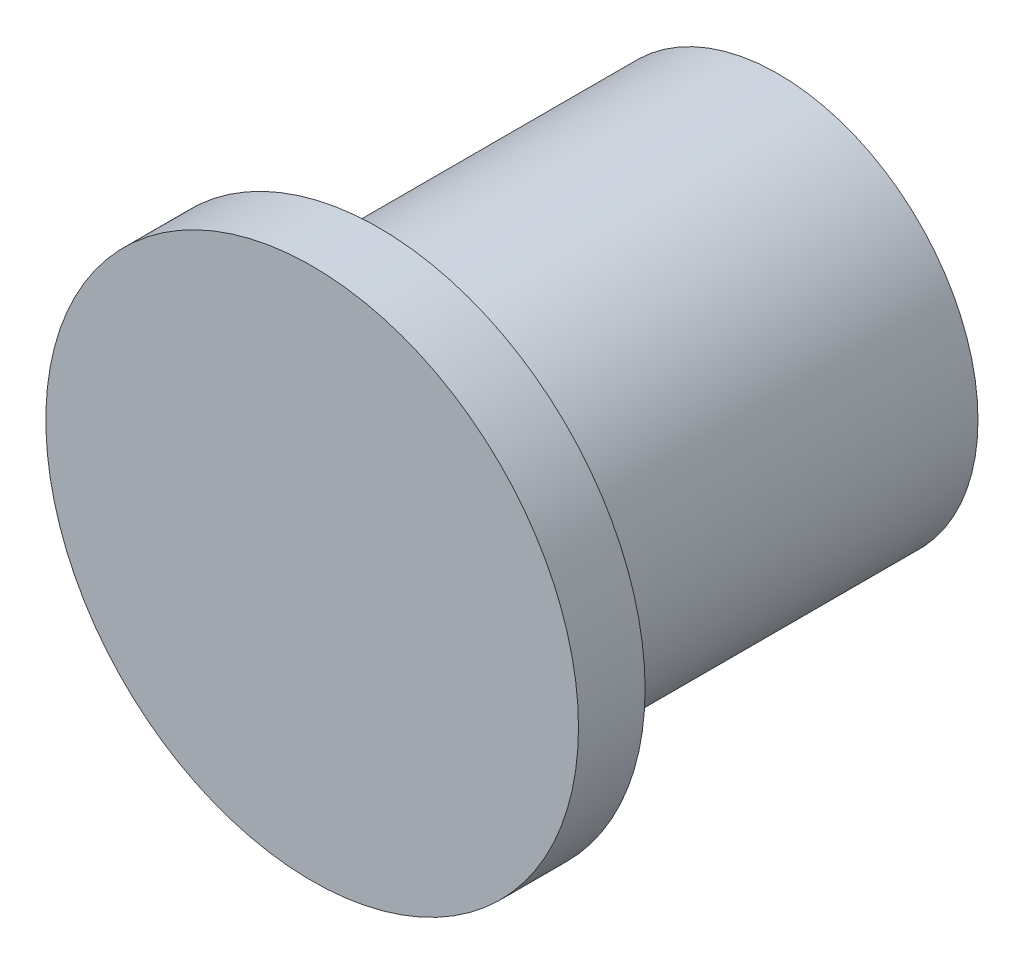
SolidWorks part; units mm, degrees
ref_plane "Front Plane" through (0, 0, 0) normal (0, 0, 1) x (1, 0, 0)
ref_plane "Top Plane" through (0, 0, 0) normal (0, 1, 0) x (1, 0, 0)
ref_plane "Right Plane" through (0, 0, 0) normal (1, 0, 0) x (0, 0, -1)
sketch "Sketch1" plane through (0, 0, 0) normal (0, 0, 1) x (1, 0, 0)
  circle A0 centre (0, 0) radius 76.2
  dimension "D1" = 152.4
extrude "Boss-Extrude1" add sketch "Sketch1" along normal blind 152.4
sketch "Sketch2" plane through (0, 0, 152.4) normal (0, 0, 1) x (1, 0, 0)
  circle A0 centre (0, 0) radius 101.6
  dimension "D1" = 203.2
extrude "Boss-Extrude2" add sketch "Sketch2" along normal blind 25.4
